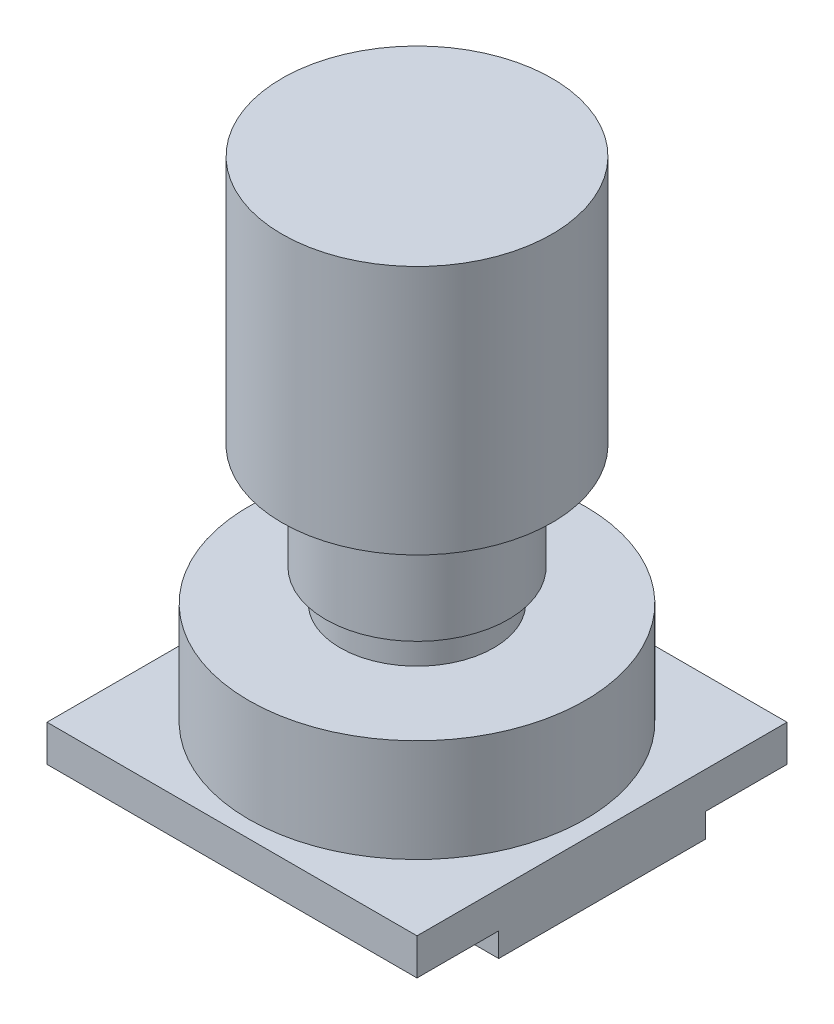
SolidWorks part; units mm, degrees
ref_plane "Front Plane" through (0, 0, 0) normal (0, 0, 1) x (1, 0, 0)
ref_plane "Top Plane" through (0, 0, 0) normal (0, 1, 0) x (1, 0, 0)
ref_plane "Right Plane" through (0, 0, 0) normal (1, 0, 0) x (0, 0, -1)
sketch "Sketch1" plane through (0, 0, 0) normal (0, 1, 0) x (1, 0, 0)
  line L1 (-19.25, -19.25) -> (19.25, -19.25)
  line L2 (-19.25, -19.25) -> (-19.25, 19.25)
  line L3 (-19.25, 19.25) -> (19.25, 19.25)
  line L4 (19.25, -19.25) -> (19.25, 19.25)
  line L5 (-19.25, -19.25) -> (19.25, 19.25) construction
  line L6 (-19.25, 19.25) -> (19.25, -19.25) construction
  point P0 (0, 0)
  dimension "D1" = 38.5
extrude "Boss-Extrude1" add sketch "Sketch1" along normal blind 3.8
sketch "Sketch2" plane through (0, 3.8, 0) normal (0, 1, 0) x (1, 0, 0)
  circle A0 centre (0, 0) radius 17.5
  dimension "D1" = 35
extrude "Boss-Extrude2" add sketch "Sketch2" along normal blind 10.7
sketch "Sketch3" plane through (0, 14.5, 0) normal (0, 1, 0) x (1, 0, 0)
  circle A0 centre (0, 0) radius 8
  dimension "D1" = 16
extrude "Boss-Extrude3" add sketch "Sketch3" along normal blind 3.3
sketch "Sketch4" plane through (0, 17.8, 0) normal (0, 1, 0) x (1, 0, 0)
  circle A0 centre (0, 0) radius 9.5
  dimension "D1" = 19
extrude "Boss-Extrude4" add sketch "Sketch4" along normal blind 11
sketch "Sketch5" plane through (0, 28.8, 0) normal (0, 1, 0) x (1, 0, 0)
  circle A0 centre (0, 0) radius 14.05
  dimension "D1" = 28.1
extrude "Boss-Extrude5" add sketch "Sketch5" along normal blind 26
sketch "Sketch7" plane through (0, 0, 0) normal (0, -1, 0) x (1, 0, 0)
  line L0 (19.25, 19.25) -> (19.25, -19.25) construction
  line L1 (19.25, -10.75) -> (13.25, -10.75)
  line L2 (19.25, -10.75) -> (19.25, 10.75)
  line L3 (19.25, 10.75) -> (13.25, 10.75)
  line L4 (13.25, -10.75) -> (13.25, 10.75)
  line L5 (19.25, -19.25) -> (-19.25, -19.25) construction
  line L6 (-19.25, 19.25) -> (19.25, 19.25) construction
  dimension "D1" = 8.5
  dimension "D2" = 8.5
  dimension "D3" = 6
extrude "Boss-Extrude6" add sketch "Sketch7" along normal blind 2.5
sketch "Sketch8" plane through (0, 0, 0) normal (0, -1, 0) x (-1, 0, 0)
  line L0 (-19.25, -19.25) -> (-15.45, -19.25) construction
  line L1 (19.25, -19.25) -> (-19.25, -19.25) construction
  line L2 (-15.45, -19.25) -> (-15.45, -15.45) construction
  line L3 (-19.25, 19.25) -> (-15.45, 19.25) construction
  line L4 (-19.25, 19.25) -> (19.25, 19.25) construction
  line L5 (-15.45, 19.25) -> (-15.45, 15.45) construction
  line L6 (19.25, -19.25) -> (19.25, -15.45) construction
  line L7 (19.25, 19.25) -> (19.25, -19.25) construction
  line L8 (19.25, -15.45) -> (15.45, -15.45) construction
  line L9 (19.25, 19.25) -> (19.25, 15.45) construction
  line L10 (19.25, 15.45) -> (15.45, 15.45) construction
  circle A0 centre (-15.45, -15.45) radius 1.35
  circle A1 centre (-15.45, 15.45) radius 1.35
  circle A2 centre (15.45, -15.45) radius 1.35
  circle A3 centre (15.45, 15.45) radius 1.35
equation "\"D1@Boss-Extrude2\"=12.2-1.5"
equation "\"D1@Boss-Extrude6\"=4-1.5"
